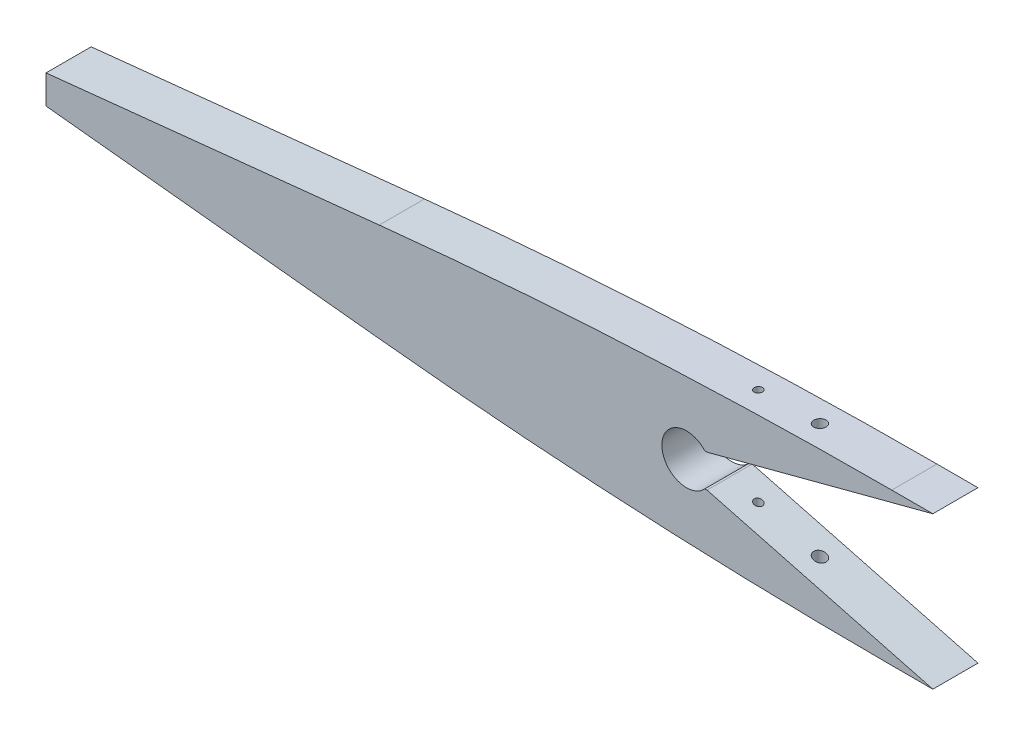
SolidWorks part; units mm, degrees
material "Beech"
ref_plane "Front Plane" through (0, 0, 0) normal (0, 0, 1) x (1, 0, 0)
ref_plane "Top Plane" through (0, 0, 0) normal (0, 1, 0) x (1, 0, 0)
ref_plane "Right Plane" through (0, 0, 0) normal (1, 0, 0) x (0, 0, -1)
sketch "Sketch1" plane through (0, 0, 0) normal (0, 0, 1) x (1, 0, 0)
  line L0 (-40, 18.5) -> (-30, 18.5)
  line L1 (-30, 18.5) -> (-85, 4)
  line L2 (-85, 4) -> (-85.5279, 4)
  line L3 (-85.5279, -4) -> (-85, -4)
  line L4 (-85, -4) -> (-30, -18.5)
  line L5 (-30, -18.5) -> (-40, -18.5)
  line L6 (-30, 18.5) -> (-30, -18.5) construction
  line L7 (-90, 0) -> (-30, 0) construction
  line L8 (-164.8278, 11.9898) -> (-246, 3.5)
  line L9 (-164.8278, -11.9898) -> (-246, -3.5)
  line L10 (-246, -3.5) -> (-246, 3.5)
  line L11 (-246, 0) -> (-90, 0) construction
  line L12 (0, 0) -> (-30, 0) construction
  arc A0 (-85.5279, 4) -> (-85.5279, -4) centre (-90, 0) ccw
  arc A1 (-40, 18.5) -> (-164.8278, 11.9898) centre (-40, -1181.5) ccw
  arc A2 (-40, -18.5) -> (-164.8278, -11.9898) centre (-40, 1181.5) cw
  dimension "D4" = 6
  dimension "D8" = 1200
  dimension "D1" = 7
  dimension "D2" = 10
  dimension "D3" = 8
  dimension "D5" = 37
  dimension "D6" = 246
  dimension "D7" = 30
  dimension "D9" = 55
  dimension "D10" = 90
extrude "Extrude1" add sketch "Sketch1" along normal mid plane 11
sketch "Sketch2" plane through (0, 0, 0) normal (0, 1, 0) x (1, 0, 0)
  line L0 (0, 0) -> (-63, 0) construction
  line L1 (-63, 0) -> (-78, 0) construction
  circle A0 centre (-63, 0) radius 1.5
  circle A1 centre (-78, 0) radius 1
  dimension "D1" = 3
  dimension "D4" = 2
  dimension "D2" = 63
  dimension "D3" = 15
extrude "Cut-Extrude1" cut sketch "Sketch2" against normal through all and the other way through all
